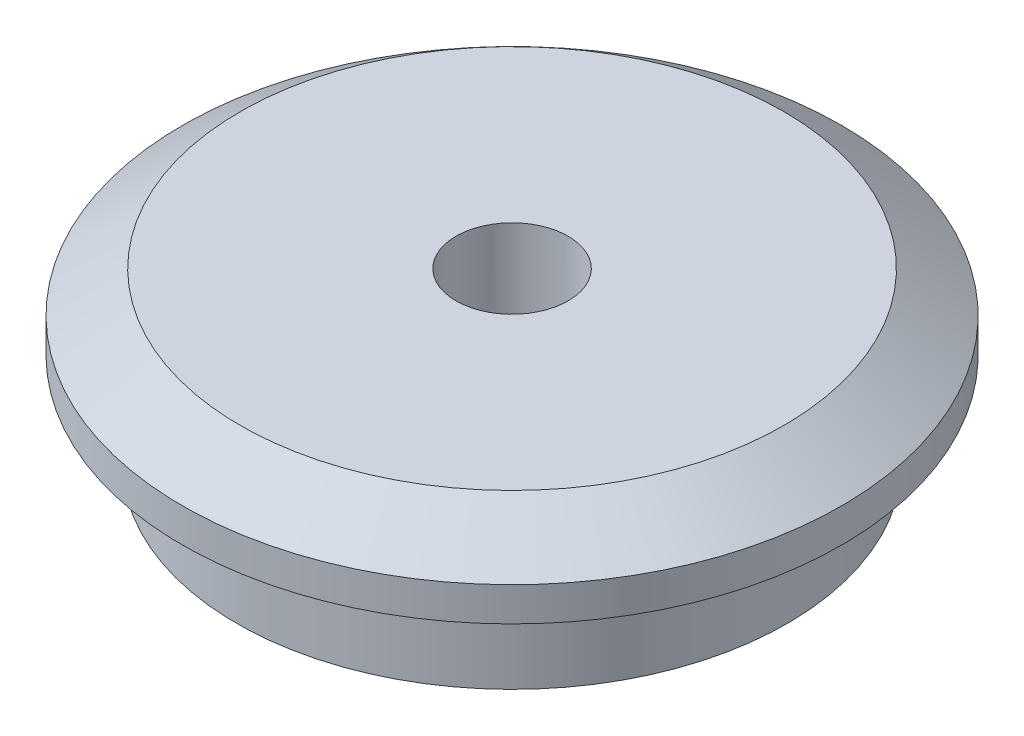
SolidWorks part; units mm, degrees
ref_plane "Front" through (0, 0, 0) normal (0, 0, 1) x (1, 0, 0)
ref_plane "Top" through (0, 0, 0) normal (0, 1, 0) x (1, 0, 0)
ref_plane "Right" through (0, 0, 0) normal (1, 0, 0) x (0, 0, -1)
sketch "Sketch1" plane through (0, 0, 0) normal (0, 0, 1) x (1, 0, 0)
  line L0 (0, 0) -> (0, 52.8355) construction
  line L1 (0, 2.2) -> (6.9, 2.2)
  line L2 (6.9, 2.2) -> (6.9, 0)
  line L3 (6.9, 0) -> (8.1, 0)
  line L4 (8.1, 0) -> (8.1, 2.8)
  line L5 (8.1, 2.8) -> (9.7, 2.8)
  line L6 (9.7, 3.8) -> (8, 5)
  line L7 (8, 5) -> (0, 5)
  line L8 (0, 5) -> (0, 2.2)
  line L9 (9.7, 2.8) -> (9.7, 3.8)
  dimension "D1" = 13.8
  dimension "D2" = 16.2
  dimension "D3" = 2.8
  dimension "D4" = 2.2
  dimension "D5" = 5
  dimension "D6" = 19.4
  dimension "D7" = 1
  dimension "D8" = 16
revolve "Revolve1" add sketch "Sketch1" angle 360 about L0
sketch "Sketch2" plane through (0, 5, 0) normal (0, 1, 0) x (1, 0, 0)
  circle A0 centre (0, 0) radius 1.65
  dimension "D1" = 3.3
extrude "Cut-Extrude1" cut sketch "Sketch2" against normal blind 10
